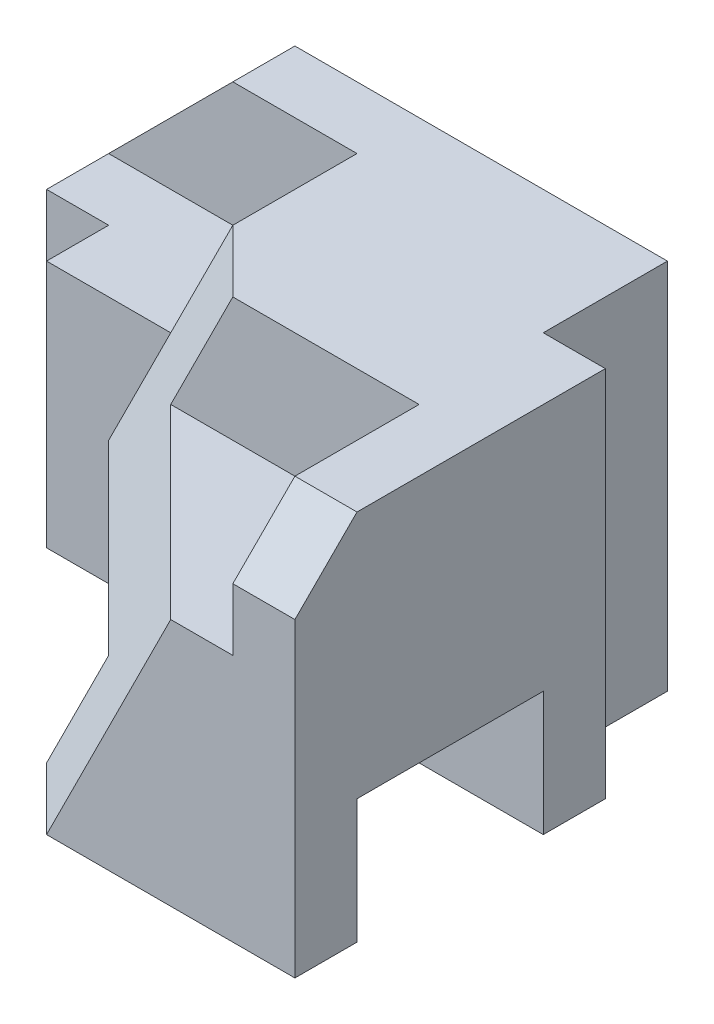
SolidWorks part; units mm, degrees
ref_plane "Front Plane" through (0, 0, 0) normal (0, 0, 1) x (1, 0, 0)
ref_plane "Top Plane" through (0, 0, 0) normal (0, 1, 0) x (1, 0, 0)
ref_plane "Right Plane" through (0, 0, 0) normal (1, 0, 0) x (0, 0, -1)
sketch "Sketch1" plane through (0, 0, 0) normal (0, 1, 0) x (1, 0, 0)
  line L1 (-4.5, -3.5) -> (4.5, -3.5)
  line L2 (-4.5, -3.5) -> (-4.5, 3.5)
  line L3 (-4.5, 3.5) -> (4.5, 3.5)
  line L4 (4.5, -3.5) -> (4.5, 3.5)
  line L5 (-4.5, -3.5) -> (4.5, 3.5) construction
  line L6 (-4.5, 3.5) -> (4.5, -3.5) construction
  point P0 (0, 0)
  dimension "D1" = 7
  dimension "D2" = 9
extrude "Boss-Extrude1" add sketch "Sketch1" along normal blind 6
sketch "Sketch2" plane through (-4.5, 0, 0) normal (-1, 0, 0) x (0, 0, 1)
  line L0 (-3.5, 0) -> (3.5, 0) construction
  line L1 (2.5, 0) -> (-0.5, 0)
  line L2 (2.5, 0) -> (2.5, 2)
  line L3 (2.5, 2) -> (-0.5, 2)
  line L4 (-0.5, 0) -> (-0.5, 2)
  line L5 (3.5, 6) -> (3.5, 0) construction
  dimension "D1" = 1
  dimension "D2" = 3
  dimension "D3" = 2
extrude "Cut-Extrude1" cut sketch "Sketch2" against normal through all
sketch "Sketch3" plane through (-4.5, 0, 0) normal (-1, 0, 0) x (0, 0, 1)
  line L1 (3.5, 6) -> (0.5, 6)
  line L2 (3.5, 6) -> (3.5, 4)
  line L3 (3.5, 4) -> (0.5, 4)
  line L4 (0.5, 6) -> (0.5, 4)
  dimension "D1" = 2
  dimension "D2" = 3
extrude "Cut-Extrude2" cut sketch "Sketch3" against normal blind 8
chamfer "Chamfer1" distance 1 distance2 1 1 edges at (4, 6, 3.5)
sketch "Sketch4" plane through (0, 6, 0) normal (0, 1, 0) x (1, 0, 0)
  line L1 (4.5, 3.5) -> (3.5, 3.5)
  line L2 (4.5, 3.5) -> (4.5, 1.5)
  line L3 (4.5, 1.5) -> (3.5, 1.5)
  line L4 (3.5, 3.5) -> (3.5, 1.5)
  dimension "D1" = 2
  dimension "D2" = 1
extrude "Cut-Extrude3" cut sketch "Sketch4" against normal through all
sketch "Sketch5" plane through (0, 6, 0) normal (0, 1, 0) x (1, 0, 0)
  line L1 (-4.5, -0.5) -> (-1.5, -0.5)
  line L2 (-4.5, -0.5) -> (-4.5, 1.5)
  line L3 (-4.5, 1.5) -> (-1.5, 1.5)
  line L4 (-1.5, -0.5) -> (-1.5, 1.5)
  dimension "D1" = 3
  dimension "D2" = 2
extrude "Cut-Extrude4" cut sketch "Sketch5" against normal blind 2
chamfer "Chamfer2" distance 2 1 edges at (-4.5, 6, -2.5)
sketch "Sketch6" plane through (0, 0, -1.5) normal (0, 0, 1) x (1, 0, 0)
  line L0 (-4.5, 4) -> (-2.5, 6)
  line L1 (-2.5, 6) -> (-0.5, 6)
  line L2 (-0.5, 6) -> (-1.5, 4)
  line L3 (-1.5, 4) -> (-4.5, 4)
  dimension "D1" = 1
extrude "Cut-Extrude5" cut sketch "Sketch6" against normal blind 1 and the other way blind 2
sketch "Sketch7" plane through (0, 4, 0) normal (0, 1, 0) x (1, 0, 0)
  line L0 (-4.5, 1.5) -> (-3.5, 1.5)
  line L1 (-4.5, 2.5) -> (-4.5, -3.5) construction
  line L2 (-3.5, 1.5) -> (-3.5, 0.5)
  line L3 (-3.5, 0.5) -> (-2.5, 0.5)
  line L4 (-2.5, 0.5) -> (-2.5, -3.5)
  line L5 (3.5, -3.5) -> (-4.5, -3.5) construction
  line L6 (-2.5, -3.5) -> (-4.5, -3.5)
  line L7 (-4.5, -3.5) -> (-4.5, 1.5)
  dimension "D1" = 1
  dimension "D2" = 4
  dimension "D3" = 1
  dimension "D4" = 1
extrude "Cut-Extrude6" cut sketch "Sketch7" against normal blind 5.0941
sketch "Sketch9" plane through (0, 4, 0) normal (0, 1, 0) x (1, 0, 0)
  line L0 (3.5, -0.5) -> (-1.5, -0.5) construction
  line L1 (3.5, -3.5) -> (-2.5, -3.5) construction
  point P0 (-0.5, -0.5)
  point P1 (2.5, -3.5)
  dimension "D1" = 1
  dimension "D2" = 4
sketch "Sketch10" plane through (0, 0, 3.5) normal (0, 0, 1) x (1, 0, 0)
  line L0 (-2.5, 0) -> (4.5, 0) construction
  point P0 (0.5, 0)
  dimension "D1" = 4
sketch "Sketch11" plane through (0, 0, 2.5) normal (0, 0, -1) x (-1, 0, 0)
  line L0 (-4.5, 0) -> (2.5, 0) construction
  line L2 (-4.5, 2) -> (2.5, 2) construction
  point P0 (0.5, 0)
  point P1 (-0.5, 2)
  dimension "D1" = 1
  dimension "D2" = 1
sketch "Sketch12" plane through (0, 0, -0.5) normal (0, 0, 1) x (1, 0, 0)
  point P0 (-2.5, 2)
sketch3d "3DSketch1"
  line L0 (2.5, 4, 3.5) -> (0.5, 0, 3.5)
  line L1 (0.5, 0, 3.5) -> (-0.5, 0, 2.5)
  line L2 (-0.5, 0, 2.5) -> (0.5, 2, 2.5)
  line L3 (0.5, 2, 2.5) -> (-2.5, 2, -0.5)
  line L4 (-0.5, 4, 0.5) -> (0.5, 6, 0.5)
  line L5 (3.5, 6, 0.5) -> (-0.5, 6, 0.5) construction
  line L6 (-0.5, 6, 0.5) -> (-0.5, 6, -2.5) construction
  line L7 (-0.5, 4, 0.5) -> (2.5, 4, 3.5)
  line L8 (0.5, 6, 0.5) -> (-0.5, 6, -0.5)
  line L9 (-0.5, 6, -0.5) -> (-2.5, 2, -0.5)
  point P19 (-0.5, 6, -0.5)
  dimension "D1" = 1
  dimension "D2" = 1
extrude "Cut-Extrude7" cut sketch "3DSketch1" along direction (1, 0, 0) on the side against the normal blind 5.0941
